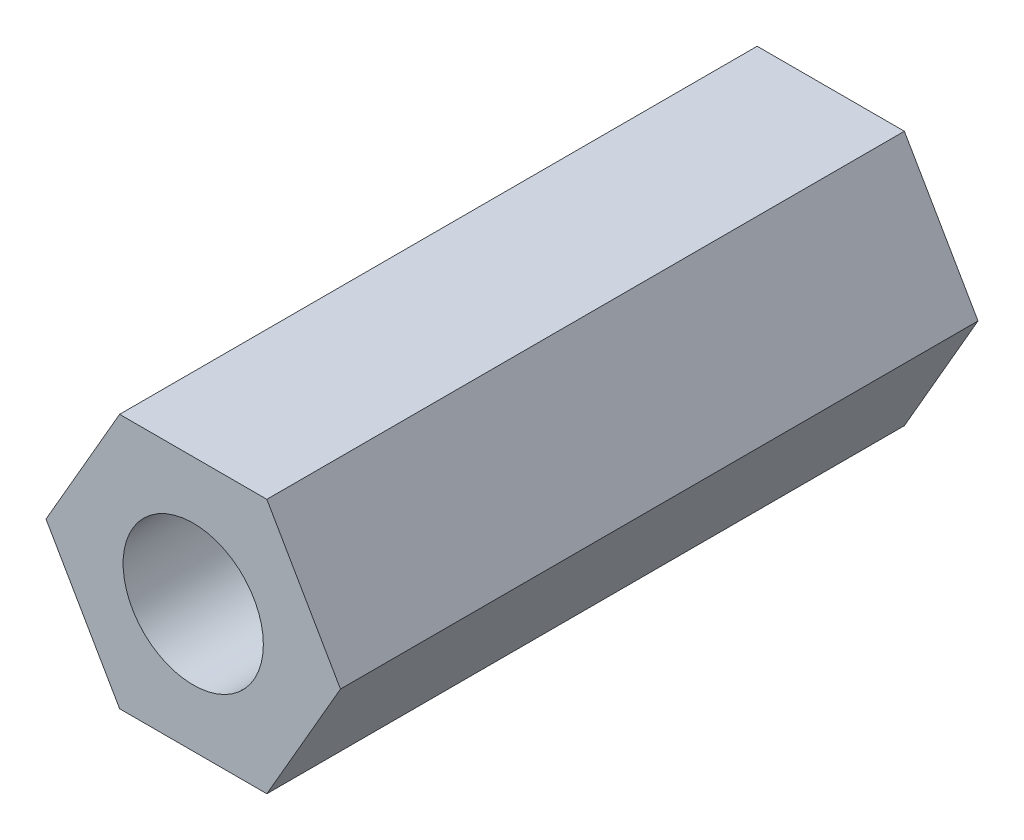
SolidWorks part; units mm, degrees
material "1060 合金"
ref_plane "前视基准面" through (0, 0, 0) normal (0, 0, 1) x (1, 0, 0)
ref_plane "上视基准面" through (0, 0, 0) normal (0, 1, 0) x (1, 0, 0)
ref_plane "右视基准面" through (0, 0, 0) normal (1, 0, 0) x (0, 0, -1)
other "Configuration Table"
sketch "草图1" plane through (0, 0, 0) normal (0, 0, 1) x (1, 0, 0)
  line L1 (-1.7321, 3) -> (-3.4641, 0)
  line L2 (-3.4641, 0) -> (-1.7321, -3)
  line L3 (-1.7321, -3) -> (1.7321, -3)
  line L4 (1.7321, -3) -> (3.4641, 0)
  line L5 (3.4641, 0) -> (1.7321, 3)
  line L6 (1.7321, 3) -> (-1.7321, 3)
  circle A0 centre (0, 0) radius 3 construction
  dimension "D1" = 6
extrude "凸台-拉伸1" add sketch "草图1" along normal blind 15
hole_wizard "M4 螺纹孔1" positions "草图2" profile "草图3" tap size "M4" standard "GB"
sketch "草图2" plane through (0, 0, 15) normal (0, 0, 1) x (1, 0, 0)
  point P0 (0, 0)
sketch "草图3" plane through (0, 0, 15) normal (1, 0, 0) x (0, -1, 0)
  line L0 (0, 0) -> (0, 18.0914)
  line L1 (0, 18.0914) -> (1.65, 17.1)
  line L2 (1.65, 17.1) -> (1.65, 0)
  line L5 (1.65, 0) -> (0, 0)
  line L10 (0, 18.0914) -> (-1.65, 17.1) construction
  line L11 (0, -6.35) -> (0, 107.95) construction
  dimension "螺纹孔钻头直径" = 3.3
  dimension "螺纹孔钻头深度" = 17.1
  dimension "导头角度" = 118
cosmetic thread "孔螺蚊线1"
